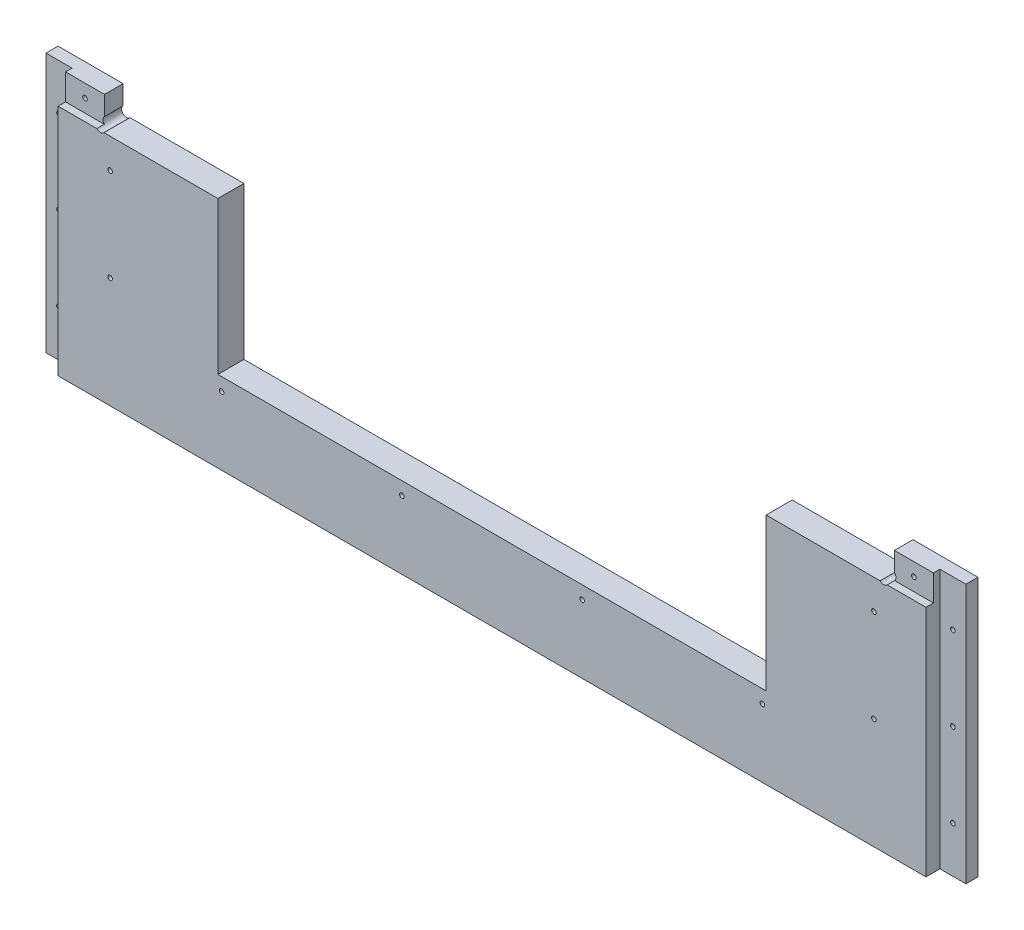
SolidWorks part; units mm, degrees
material "Pine"
ref_plane "Front Plane" through (0, 0, 0) normal (0, 0, 1) x (1, 0, 0)
ref_plane "Top Plane" through (0, 0, 0) normal (0, 1, 0) x (1, 0, 0)
ref_plane "Right Plane" through (0, 0, 0) normal (1, 0, 0) x (0, 0, -1)
sketch "Sketch1" plane through (0, 0, 0) normal (0, 0, 1) x (1, 0, 0)
  line L0 (8932.6508, -5243.5125) -> (10226.1458, -5243.5125)
  line L1 (9086.3208, -4722.0918) -> (10222.9708, -4853.7812)
  line L2 (8914.8708, -6342.0625) -> (10197.5708, -6342.0625)
  line L3 (8914.8708, -5808.6625) -> (10197.5708, -5808.6625)
  line L4 (8919.6333, -5253.0375) -> (10218.2083, -5253.0375)
  line L5 (9134.2633, -4656.1375) -> (9134.2633, -4638.3575)
  line L6 (9091.0833, -4638.3575) -> (9134.2633, -4638.3575)
  line L7 (9091.0833, -4567.2375) -> (9091.0833, -4638.3575)
  line L8 (9134.2633, -4656.1375) -> (9581.3033, -4656.1375)
  line L9 (9091.0833, -4567.2375) -> (9624.4833, -4567.2375)
  line L10 (9581.3033, -4656.1375) -> (9581.3033, -4638.3575)
  line L11 (9581.3033, -4638.3575) -> (9624.4833, -4638.3575)
  line L12 (9624.4833, -4567.2375) -> (9624.4833, -4638.3575)
  line L13 (8932.6508, -5225.7325) -> (9344.9775, -5225.7325)
  line L14 (8932.6508, -5256.2125) -> (8932.6508, -5243.5125)
  line L15 (8911.6958, -5256.2125) -> (8932.6508, -5256.2125)
  line L16 (8914.8708, -4722.0918) -> (9086.3208, -4722.0918)
  line L17 (8911.6958, -4715.5913) -> (8932.6508, -4715.5913)
  line L18 (8914.8708, -6342.0625) -> (8914.8708, -5808.6625)
  line L19 (12082.9917, -4722.0918) -> (10946.3417, -4853.7812)
  line L20 (12236.6617, -5243.5125) -> (10943.1667, -5243.5125)
  line L21 (10951.1042, -5253.0375) -> (12249.6792, -5253.0375)
  line L22 (10838.3917, -5656.2625) -> (11308.2917, -5656.2625)
  line L23 (10838.3917, -5719.7625) -> (11308.2917, -5719.7625)
  line L24 (10838.3917, -5742.5368) -> (11308.2917, -5742.5368)
  line L25 (10806.6417, -6342.0625) -> (11340.0417, -6342.0625)
  line L26 (10803.4667, -6335.7125) -> (11343.2167, -6335.7125)
  line L27 (10803.4667, -6317.9325) -> (11343.2167, -6317.9325)
  line L28 (10943.1667, -5225.7325) -> (11376.4483, -5225.7325)
  line L29 (11506.7292, -4754.5625) -> (10806.6417, -4827.5875)
  line L30 (11506.7292, -4567.2375) -> (11506.7292, -4754.5625)
  line L31 (10806.6417, -4567.2375) -> (10806.6417, -4827.5875)
  line L32 (10806.6417, -4567.2375) -> (11506.7292, -4567.2375)
  line L33 (10235.6708, -6329.3625) -> (10245.1958, -6329.3625)
  line L34 (10245.1958, -6329.3625) -> (10254.7208, -6278.5625)
  line L35 (10302.3458, -6329.3625) -> (10311.8708, -6278.5625)
  line L36 (10302.3458, -6329.3625) -> (10292.8208, -6329.3625)
  line L37 (10245.1958, -5821.3625) -> (10254.7208, -5872.1625)
  line L38 (10235.6708, -5821.3625) -> (10245.1958, -5821.3625)
  line L39 (10292.8208, -5821.3625) -> (10302.3458, -5821.3625)
  line L40 (10302.3458, -5821.3625) -> (10311.8708, -5872.1625)
  line L41 (10235.6708, -5821.3625) -> (10235.6708, -6329.3625)
  line L42 (10254.7208, -5872.1625) -> (10254.7208, -6278.5625)
  line L43 (10311.8708, -5872.1625) -> (10311.8708, -6278.5625)
  line L44 (10292.8208, -5821.3625) -> (10292.8208, -6329.3625)
  line L45 (8932.6508, -5225.7325) -> (8932.6508, -4715.5913)
  line L46 (8911.6958, -4715.5913) -> (8911.6958, -5256.2125)
  line L47 (8914.8708, -5248.275) -> (8914.8708, -4722.0918)
  line L48 (8919.6333, -5253.0375) -> (8914.8708, -5248.275)
  line L49 (8914.8708, -5145.0875) -> (8937.426, -5145.0875)
  line L50 (8914.8708, -5202.2375) -> (8937.426, -5202.2375)
  line L51 (10838.3917, -5656.2625) -> (10838.3917, -5719.7625)
  line L52 (10832.0417, -5736.1868) -> (10856.1717, -5736.1868)
  line L53 (10806.6417, -6342.0625) -> (10806.6417, -5818.7368)
  line L54 (10832.0417, -5649.9125) -> (10856.1717, -5649.9125)
  line L55 (10832.0417, -5726.1125) -> (10856.1717, -5726.1125)
  line L56 (10806.6417, -5818.7368) -> (10833.9015, -5818.7368)
  line L57 (10832.0417, -5806.0442) -> (10851.6815, -5806.0442)
  line L58 (10856.1717, -5801.5541) -> (10856.1717, -5736.1868)
  line L59 (10838.3917, -5814.2467) -> (10838.3917, -5742.5368)
  line L60 (10832.0417, -5806.0442) -> (10832.0417, -5736.1868)
  line L61 (10803.4667, -6317.9325) -> (10803.4667, -6335.7125)
  line L62 (10197.5708, -5808.6625) -> (10197.5708, -6342.0625)
  line L63 (9762.3842, -6348.4125) -> (9762.3842, -5802.3125)
  line L64 (9780.1642, -6348.4125) -> (9762.3842, -6348.4125)
  line L65 (9780.1642, -5802.3125) -> (9780.1642, -6348.4125)
  line L66 (9762.3842, -5802.3125) -> (9780.1642, -5802.3125)
  line L67 (9332.2775, -6348.4125) -> (9332.2775, -5802.3125)
  line L68 (9332.2775, -6348.4125) -> (9350.0575, -6348.4125)
  line L69 (9350.0575, -5802.3125) -> (9350.0575, -6348.4125)
  line L70 (9332.2775, -5802.3125) -> (9350.0575, -5802.3125)
  line L71 (9993.8374, -6061.075) -> (9993.8374, -6045.2418)
  line L72 (9998.5999, -6065.8375) -> (10014.4331, -6065.8375)
  line L73 (9998.5999, -6084.8875) -> (10014.4331, -6084.8875)
  line L74 (9993.8374, -6105.4832) -> (9993.8374, -6089.65)
  line L75 (9974.7874, -6105.4832) -> (9974.7874, -6089.65)
  line L76 (9954.1917, -6084.8875) -> (9970.0249, -6084.8875)
  line L77 (9974.7874, -6061.075) -> (9974.7874, -6045.2418)
  line L78 (9954.1917, -6065.8375) -> (9970.0249, -6065.8375)
  line L79 (10793.9417, -6237.2875) -> (10816.4969, -6237.2875)
  line L80 (10793.9417, -6294.4375) -> (10816.4969, -6294.4375)
  line L81 (10856.1717, -5649.9125) -> (10856.1717, -5726.1125)
  line L82 (10832.0417, -5726.1125) -> (10832.0417, -5649.9125)
  line L83 (10226.1458, -5225.7325) -> (10226.1458, -5243.5125)
  line L84 (10205.1908, -5257.8) -> (10205.1908, -4844.2499)
  line L85 (10230.9083, -4844.2499) -> (10230.9083, -5257.8)
  line L86 (10205.1908, -5257.8) -> (10230.9083, -5257.8)
  line L87 (10205.1908, -4844.2499) -> (10230.9083, -4844.2499)
  line L88 (10946.3417, -5176.8375) -> (10968.8969, -5176.8375)
  line L89 (9349.4676, -5141.9125) -> (9358.2674, -5141.9125)
  line L90 (10946.3417, -5119.6875) -> (10968.8969, -5119.6875)
  line L91 (9929.011, -4660.9635) -> (10066.0807, -4660.9635)
  line L92 (9929.011, -4678.7435) -> (10066.0807, -4678.7435)
  line L93 (10943.1667, -5225.7325) -> (10943.1667, -5243.5125)
  line L94 (10946.3417, -5248.275) -> (10951.1042, -5253.0375)
  line L95 (10946.3417, -5257.8063) -> (10946.3417, -4849.0188)
  line L96 (10964.1217, -5257.8) -> (10964.1217, -4844.2499)
  line L97 (10938.4042, -4844.2499) -> (10938.4042, -5257.8)
  line L98 (10938.4042, -5257.8) -> (10964.1217, -5257.8)
  line L99 (10964.1217, -4844.2499) -> (10938.4042, -4844.2499)
  line L100 (10344.8908, -4560.8875) -> (10369.0208, -4560.8875)
  line L101 (10344.8908, -4560.8875) -> (10369.0208, -4560.8875)
  line L102 (10800.2917, -4560.8875) -> (10824.4217, -4560.8875)
  line L103 (10200.4156, -5119.6875) -> (10222.9708, -5119.6875)
  line L104 (10200.4156, -5176.8375) -> (10222.9708, -5176.8375)
  line L105 (9344.9775, -5146.4026) -> (9344.9775, -5225.7325)
  line L106 (10344.8908, -4560.8875) -> (10344.8908, -4833.9375)
  line L107 (9792.8642, -5225.7325) -> (9792.8642, -5146.4026)
  line L108 (9362.7575, -5225.7325) -> (9775.0842, -5225.7325)
  line L109 (9680.3633, -4761.8396) -> (9680.3633, -4559.9604)
  line L110 (9656.2333, -4559.9604) -> (9680.3633, -4559.9604)
  line L111 (9656.2333, -4761.8396) -> (9680.3633, -4761.8396)
  line L112 (9656.2333, -4761.8396) -> (9656.2333, -4559.9604)
  line L113 (9779.5743, -5141.9125) -> (9788.374, -5141.9125)
  line L114 (10070.5708, -4665.4536) -> (10070.5708, -4674.2534)
  line L115 (9924.5208, -4674.2534) -> (9924.5208, -4665.4536)
  line L116 (12127.4417, -6188.3925) -> (12205.5015, -6188.3925)
  line L117 (12209.9917, -6170.6125) -> (12209.9917, -6183.9024)
  line L118 (9792.8642, -5225.7325) -> (10226.1458, -5225.7325)
  line L119 (9662.5833, -4754.5625) -> (10362.6708, -4827.5875)
  line L120 (9662.5833, -4567.2375) -> (9662.5833, -4754.5625)
  line L121 (10362.6708, -4567.2375) -> (10362.6708, -4827.5875)
  line L122 (9662.5833, -4567.2375) -> (10362.6708, -4567.2375)
  line L123 (10824.4217, -4833.9375) -> (10800.2917, -4833.9375)
  line L124 (10800.2917, -4833.9375) -> (10800.2917, -4560.8875)
  line L125 (10824.4217, -4560.8875) -> (10824.4217, -4833.9375)
  line L126 (10344.8908, -4833.9375) -> (10369.0208, -4833.9375)
  line L127 (10369.0208, -4833.9375) -> (10369.0208, -4560.8875)
  line L128 (10222.9708, -5248.275) -> (10218.2083, -5253.0375)
  line L129 (10222.9708, -5257.8063) -> (10222.9708, -4849.0188)
  line L130 (11734.6544, -5701.375) -> (11739.2301, -5701.375)
  line L131 (9362.7575, -5225.7325) -> (9362.7575, -5146.4026)
  line L132 (9775.0842, -5146.4026) -> (9775.0842, -5225.7325)
  line L133 (11761.3864, -5701.375) -> (11756.8282, -5701.375)
  line L134 (11734.6544, -5693.755) -> (11739.2301, -5693.755)
  line L135 (11761.4039, -5693.755) -> (11756.8282, -5693.755)
  line L136 (11734.6544, -5701.375) -> (11739.2301, -5701.375)
  line L137 (11744.3462, -5721.3024) -> (11744.3462, -5706.4179)
  line L138 (11751.7122, -5721.3024) -> (11751.7122, -5706.4179)
  line L139 (11740.0917, -6170.6125) -> (11740.0917, -6183.9024)
  line L140 (11689.2917, -6188.3925) -> (11822.6417, -6188.3925)
  line L141 (11689.2917, -6348.4093) -> (11689.2917, -6164.2657)
  line L142 (11689.2917, -6164.2657) -> (11746.4417, -6164.2657)
  line L143 (11746.4417, -6164.2657) -> (11746.4417, -6188.3925)
  line L144 (11689.2917, -6164.2657) -> (11746.4417, -6164.2657)
  line L145 (11340.0417, -5818.7368) -> (11340.0417, -6342.0625)
  line L146 (11290.5117, -5726.1125) -> (11314.6417, -5726.1125)
  line L147 (11290.5117, -5649.9125) -> (11290.5117, -5726.1125)
  line L148 (11340.0417, -5818.7368) -> (11312.7818, -5818.7368)
  line L149 (11314.6417, -5806.0442) -> (11295.0018, -5806.0442)
  line L150 (11290.5117, -5801.5541) -> (11290.5117, -5736.1868)
  line L151 (11308.2917, -5814.2467) -> (11308.2917, -5742.5368)
  line L152 (11314.6417, -5806.0442) -> (11314.6417, -5736.1868)
  line L153 (11290.5117, -5736.1868) -> (11314.6417, -5736.1868)
  line L154 (11848.0417, -6267.1325) -> (11962.3417, -6267.1325)
  line L155 (11962.3417, -6267.1325) -> (11962.3417, -6203.6325)
  line L156 (11343.2167, -6317.9325) -> (11343.2167, -6335.7125)
  line L157 (11365.4417, -5656.2625) -> (11365.4417, -5719.7625)
  line L158 (11365.4417, -5656.2625) -> (11479.7417, -5656.2625)
  line L159 (11778.1917, -6071.3937) -> (11802.3217, -6071.3937)
  line L160 (11314.6417, -5726.1125) -> (11314.6417, -5649.9125)
  line L161 (11314.6417, -5649.9125) -> (11290.5117, -5649.9125)
  line L162 (11308.2917, -5719.7625) -> (11308.2917, -5656.2625)
  line L163 (11689.2917, -6348.4093) -> (11713.4217, -6348.4093)
  line L164 (12203.6417, -6164.2657) -> (12260.7917, -6164.2657)
  line L165 (11713.4217, -6348.4093) -> (11713.4217, -6164.2657)
  line L166 (11695.6417, -6342.0625) -> (11695.6417, -6170.6125)
  line L167 (11695.6417, -6048.5337) -> (11699.4517, -6052.3437)
  line L168 (11822.6417, -6292.5325) -> (11822.6417, -6188.3925)
  line L169 (11695.6417, -6342.0625) -> (11695.6417, -6170.6125)
  line L170 (11848.0417, -6203.6325) -> (11962.3417, -6203.6325)
  line L171 (11848.0417, -6203.6325) -> (11848.0417, -6267.1325)
  line L172 (11987.7417, -6267.1325) -> (11987.7417, -6203.6325)
  line L173 (11784.5417, -6077.7437) -> (11784.5417, -6141.2438)
  line L174 (11517.8417, -5656.2625) -> (11632.1417, -5656.2625)
  line L175 (11632.1417, -5656.2625) -> (11632.1417, -5719.7625)
  line L176 (11632.1417, -5719.7625) -> (11517.8417, -5719.7625)
  line L177 (11517.8417, -5719.7625) -> (11517.8417, -5656.2625)
  line L178 (11692.4667, -6028.2137) -> (11692.4667, -6045.9937)
  line L179 (11695.6417, -5979.3188) -> (11718.1969, -5979.3188)
  line L180 (11695.6417, -5922.1687) -> (11718.1969, -5922.1687)
  line L181 (11821.0415, -5722.9375) -> (11821.0415, -5943.6)
  line L182 (11687.7042, -5651.5) -> (11701.9917, -5651.5)
  line L183 (11687.7042, -5651.5) -> (11687.7042, -6055.5251)
  line L184 (11687.7042, -6055.5251) -> (11701.9917, -6055.5251)
  line L185 (11701.9917, -6055.5251) -> (11701.9917, -5651.5)
  line L186 (11695.6417, -6055.2013) -> (11695.6417, -5649.595)
  line L187 (11695.6417, -5656.2625) -> (11695.6417, -6048.5337)
  line L188 (11695.6417, -6170.6125) -> (11740.0917, -6170.6125)
  line L189 (12203.6417, -6164.2657) -> (12203.6417, -6188.3925)
  line L190 (12254.4417, -6342.0625) -> (12254.4417, -6170.6125)
  line L191 (12129.0419, -5943.6) -> (12129.0419, -5722.9375)
  line L192 (12254.4417, -6048.5337) -> (12250.6317, -6052.3437)
  line L193 (12257.6167, -6045.9937) -> (12257.6167, -6028.2137)
  line L194 (12248.0917, -5651.5) -> (12262.3792, -5651.5)
  line L195 (12262.3792, -5651.5) -> (12262.3792, -6055.5251)
  line L196 (12262.3792, -6055.5251) -> (12248.0917, -6055.5251)
  line L197 (12248.0917, -6055.5251) -> (12248.0917, -5651.5)
  line L198 (12254.4417, -6141.2438) -> (12254.4417, -6077.7437)
  line L199 (12236.6617, -6164.2657) -> (12260.7917, -6164.2657)
  line L200 (12102.0417, -6267.1325) -> (11987.7417, -6267.1325)
  line L201 (11330.1865, -6237.2875) -> (11352.7417, -6237.2875)
  line L202 (11330.1865, -6294.4375) -> (11352.7417, -6294.4375)
  line L203 (11474.6617, -5851.8425) -> (11492.4417, -5851.8425)
  line L204 (11474.6617, -5808.6625) -> (11474.6617, -5851.8425)
  line L205 (11403.5417, -5808.6625) -> (11474.6617, -5808.6625)
  line L206 (11492.4417, -5851.8425) -> (11492.4417, -6298.8825)
  line L207 (11403.5417, -6342.0625) -> (11403.5417, -5808.6625)
  line L208 (11474.6617, -6298.8825) -> (11492.4417, -6298.8825)
  line L209 (11474.6617, -6342.0625) -> (11474.6617, -6298.8825)
  line L210 (11403.5417, -6342.0625) -> (11474.6617, -6342.0625)
  line L211 (11619.4417, -5851.8425) -> (11601.6617, -5851.8425)
  line L212 (11601.6617, -5808.6625) -> (11601.6617, -5851.8425)
  line L213 (11530.5417, -5808.6625) -> (11601.6617, -5808.6625)
  line L214 (11619.4417, -5851.8425) -> (11619.4417, -6298.8825)
  line L215 (11530.5417, -6342.0625) -> (11530.5417, -5808.6625)
  line L216 (11619.4417, -6298.8825) -> (11601.6617, -6298.8825)
  line L217 (11601.6617, -6342.0625) -> (11601.6617, -6298.8825)
  line L218 (11530.5417, -6342.0625) -> (11601.6617, -6342.0625)
  line L219 (11479.7417, -5719.7625) -> (11479.7417, -5656.2625)
  line L220 (11365.4417, -5719.7625) -> (11479.7417, -5719.7625)
  line L221 (11778.1917, -6147.5937) -> (11802.3217, -6147.5937)
  line L222 (11802.3217, -6071.3937) -> (11802.3217, -6147.5937)
  line L223 (11778.1917, -6147.5937) -> (11778.1917, -6071.3937)
  line L224 (12254.4417, -5922.1687) -> (12231.8865, -5922.1687)
  line L225 (12254.4417, -5979.3188) -> (12231.8865, -5979.3188)
  line L226 (12254.4417, -6055.2013) -> (12254.4417, -5649.595)
  line L227 (12254.4417, -6048.5337) -> (12254.4417, -5656.2625)
  line L228 (11841.6917, -5702.2873) -> (12108.3917, -5702.2873)
  line L229 (11822.6417, -6292.5325) -> (12127.4417, -6292.5325)
  line L230 (12127.4417, -6292.5325) -> (12127.4417, -6188.3925)
  line L231 (12254.4417, -6170.6125) -> (12209.9917, -6170.6125)
  line L232 (11695.6417, -6342.0625) -> (12254.4417, -6342.0625)
  line L233 (12236.6617, -6348.4093) -> (12260.7917, -6348.4093)
  line L234 (12260.7917, -6348.4093) -> (12260.7917, -6164.2657)
  line L235 (12236.6617, -6348.4093) -> (12236.6617, -6164.2657)
  line L236 (12102.0417, -6203.6325) -> (12102.0417, -6267.1325)
  line L237 (11987.7417, -6203.6325) -> (12102.0417, -6203.6325)
  line L238 (12236.6617, -6147.5937) -> (12236.6617, -6071.3937)
  line L239 (12203.6417, -6188.3925) -> (12260.7917, -6188.3925)
  line L240 (11098.7417, -4665.4536) -> (11098.7417, -4674.2534)
  line L241 (11394.2283, -5146.4026) -> (11394.2283, -5225.7325)
  line L242 (11376.4483, -5225.7325) -> (11376.4483, -5146.4026)
  line L243 (11394.2283, -5225.7325) -> (11806.555, -5225.7325)
  line L244 (11841.6917, -5964.2502) -> (12108.3917, -5964.2502)
  line L245 (12236.6617, -6147.5937) -> (12260.7917, -6147.5937)
  line L246 (12236.6617, -5256.2125) -> (12236.6617, -5243.5125)
  line L247 (12260.7917, -6147.5937) -> (12260.7917, -6071.3937)
  line L248 (12260.7917, -6071.3937) -> (12236.6617, -6071.3937)
  line L249 (12254.4417, -6077.7437) -> (11784.5417, -6077.7437)
  line L250 (11784.5417, -6141.2438) -> (12254.4417, -6141.2438)
  line L252 (12254.4417, -5656.2625) -> (11695.6417, -5656.2625)
  line L253 (11699.4517, -6052.3437) -> (12250.6317, -6052.3437)
  line L254 (11692.4667, -6045.9937) -> (12257.6167, -6045.9937)
  line L255 (11692.4667, -6028.2137) -> (12257.6167, -6028.2137)
  line L256 (11824.335, -5146.4026) -> (11824.335, -5225.7325)
  line L257 (11811.0451, -5141.9125) -> (11819.8449, -5141.9125)
  line L258 (11244.7917, -4674.2534) -> (11244.7917, -4665.4536)
  line L259 (11806.555, -5225.7325) -> (11806.555, -5146.4026)
  line L260 (11488.9492, -4761.8396) -> (11488.9492, -4559.9604)
  line L261 (11488.9492, -4559.9604) -> (11513.0792, -4559.9604)
  line L262 (11488.9492, -4761.8396) -> (11513.0792, -4761.8396)
  line L263 (11513.0792, -4761.8396) -> (11513.0792, -4559.9604)
  line L264 (11240.3015, -4660.9635) -> (11103.2318, -4660.9635)
  line L265 (11103.2318, -4678.7435) -> (11240.3015, -4678.7435)
  line L266 (12236.6617, -5225.7325) -> (12236.6617, -4715.5913)
  line L267 (12257.6167, -4715.5913) -> (12257.6167, -5256.2125)
  line L268 (12254.4417, -5248.275) -> (12254.4417, -4722.0918)
  line L269 (12236.6617, -5225.7325) -> (11824.335, -5225.7325)
  line L270 (12035.0492, -4656.1375) -> (12035.0492, -4638.3575)
  line L271 (12078.2292, -4638.3575) -> (12035.0492, -4638.3575)
  line L272 (12078.2292, -4567.2375) -> (12078.2292, -4638.3575)
  line L273 (12035.0492, -4656.1375) -> (11588.0092, -4656.1375)
  line L274 (11544.8292, -4567.2375) -> (12078.2292, -4567.2375)
  line L275 (11588.0092, -4656.1375) -> (11588.0092, -4638.3575)
  line L276 (11544.8292, -4638.3575) -> (11588.0092, -4638.3575)
  line L277 (11544.8292, -4567.2375) -> (11544.8292, -4638.3575)
  line L278 (12249.6792, -5253.0375) -> (12254.4417, -5248.275)
  line L280 (12257.6167, -5256.2125) -> (12236.6617, -5256.2125)
  line L281 (12231.8865, -5145.0875) -> (12254.4417, -5145.0875)
  line L282 (12231.8865, -5202.2375) -> (12254.4417, -5202.2375)
  line L283 (12236.6617, -4715.5913) -> (12257.6167, -4715.5913)
  line L284 (12082.9917, -4722.0918) -> (12254.4417, -4722.0918)
  line L285 (11380.9385, -5141.9125) -> (11389.7382, -5141.9125)
  circle A0 centre (8923.7608, -4778.9042) radius 1.5875
  circle A1 centre (9062.6598, -4736.3765) radius 2.3685
  circle A2 centre (9051.3958, -6281.7375) radius 22.225
  circle A3 centre (9083.1458, -6249.9875) radius 1.5875
  circle A4 centre (9083.1458, -6313.4875) radius 1.5875
  circle A5 centre (9019.6458, -6249.9875) radius 1.5875
  circle A6 centre (9019.6458, -6313.4875) radius 1.5875
  circle A7 centre (8972.3383, -5202.2375) radius 1.5875
  circle A8 centre (8923.7608, -5015.9708) radius 1.5875
  circle A9 centre (8923.7608, -5134.5042) radius 1.5875
  circle A10 centre (9054.5708, -5234.6225) radius 1.5875
  circle A11 centre (8923.7608, -4897.4375) radius 1.5875
  circle A12 centre (8972.3383, -5087.9375) radius 1.5875
  circle A13 centre (8972.3383, -5145.0875) radius 1.5875
  circle A14 centre (10847.2817, -5668.9625) radius 1.5875
  circle A15 centre (10847.2817, -5707.0625) radius 1.5875
  circle A16 centre (10847.2817, -5755.2368) radius 1.5875
  circle A17 centre (10851.4092, -6237.2875) radius 1.5875
  circle A18 centre (10851.4092, -6294.4375) radius 1.5875
  circle A19 centre (10847.2817, -5793.3442) radius 1.5875
  arc A20 (10833.9015, -5818.7368) -> (10838.3917, -5814.2467) centre (10836.1466, -5816.4918) ccw
  arc A21 (10851.6815, -5806.0442) -> (10856.1717, -5801.5541) centre (10853.9266, -5803.7992) ccw
  circle A22 centre (10882.8417, -6040.4375) radius 1.5875
  circle A23 centre (10882.8417, -6218.2375) radius 1.5875
  circle A24 centre (10882.8417, -5862.6375) radius 1.5875
  circle A25 centre (10908.2417, -6326.8225) radius 1.5875
  circle A26 centre (10908.2417, -6326.8225) radius 1.5875
  circle A27 centre (10851.4092, -6180.1375) radius 1.5875
  circle A28 centre (10815.5317, -4783.4231) radius 1.5875
  circle A29 centre (10815.5317, -4696.9488) radius 1.5875
  circle A30 centre (10815.5317, -4610.4746) radius 1.5875
  circle A31 centre (10979.1323, -4867.0082) radius 2.3685
  circle A32 centre (10190.1802, -4867.0082) radius 2.3685
  circle A33 centre (10955.2317, -4929.9812) radius 1.5875
  circle A34 centre (10955.2317, -5031.5812) radius 1.5875
  circle A35 centre (10214.0808, -4929.9812) radius 1.5875
  circle A36 centre (10214.0808, -5031.5812) radius 1.5875
  circle A37 centre (9341.1675, -6265.8625) radius 1.5875
  circle A38 centre (9771.2742, -5884.8625) radius 1.5875
  circle A39 centre (9771.2742, -6138.8625) radius 1.5875
  circle A40 centre (9771.2742, -6011.8625) radius 1.5875
  arc A41 (10036.2287, -6113.8083) -> (10051.3426, -6111.6033) centre (10042.9639, -6107.0732) ccw
  arc A42 (10051.3426, -6111.6033) -> (10051.3426, -6039.1217) centre (9984.3124, -6075.3625) ccw
  arc A43 (10051.3426, -6039.1217) -> (10036.2287, -6036.9167) centre (10042.9639, -6043.6518) ccw
  arc A44 (10034.5851, -6102.5431) -> (10034.5851, -6048.1819) centre (9984.3124, -6075.3625) ccw
  arc A45 (10034.5851, -6102.5431) -> (10036.2287, -6113.8083) centre (10042.9639, -6107.0732) ccw
  arc A46 (10036.2287, -6036.9167) -> (10034.5851, -6048.1819) centre (10042.9639, -6043.6518) ccw
  arc A47 (9945.8666, -6127.2787) -> (9948.0717, -6142.3927) centre (9952.6018, -6134.0139) ccw
  arc A48 (9948.0717, -6142.3927) -> (10020.5532, -6142.3927) centre (9984.3124, -6075.3625) ccw
  arc A49 (10020.5532, -6142.3927) -> (10022.7583, -6127.2787) centre (10016.0231, -6134.0139) ccw
  arc A50 (9957.1319, -6125.6352) -> (10011.493, -6125.6352) centre (9984.3124, -6075.3625) ccw
  arc A51 (9957.1319, -6125.6352) -> (9945.8666, -6127.2787) centre (9952.6018, -6134.0139) ccw
  arc A52 (10022.7583, -6127.2787) -> (10011.493, -6125.6352) centre (10016.0231, -6134.0139) ccw
  arc A53 (9932.3962, -6036.9167) -> (9917.2822, -6039.1217) centre (9925.661, -6043.6518) ccw
  arc A54 (9917.2822, -6039.1217) -> (9917.2822, -6111.6033) centre (9984.3124, -6075.3625) ccw
  arc A55 (9917.2822, -6111.6033) -> (9932.3962, -6113.8083) centre (9925.661, -6107.0732) ccw
  arc A56 (9934.0398, -6048.1819) -> (9934.0398, -6102.5431) centre (9984.3124, -6075.3625) ccw
  arc A57 (9934.0398, -6048.1819) -> (9932.3962, -6036.9167) centre (9925.661, -6043.6518) ccw
  arc A58 (9932.3962, -6113.8083) -> (9934.0398, -6102.5431) centre (9925.661, -6107.0732) ccw
  arc A59 (9945.8666, -6023.4463) -> (9957.1319, -6025.0898) centre (9952.6018, -6016.7111) ccw
  arc A60 (10011.493, -6025.0898) -> (10022.7583, -6023.4463) centre (10016.0231, -6016.7111) ccw
  arc A61 (10011.493, -6025.0898) -> (9957.1319, -6025.0898) centre (9984.3124, -6075.3625) ccw
  arc A62 (9948.0717, -6008.3323) -> (9945.8666, -6023.4463) centre (9952.6018, -6016.7111) ccw
  arc A63 (10020.5532, -6008.3323) -> (9948.0717, -6008.3323) centre (9984.3124, -6075.3625) ccw
  arc A64 (10022.7583, -6023.4463) -> (10020.5532, -6008.3323) centre (10016.0231, -6016.7111) ccw
  arc A65 (10005.0943, -6187.7574) -> (10096.7073, -6096.1443) centre (9984.3124, -6075.3625) ccw
  arc A66 (9993.8374, -6178.3911) -> (10005.0943, -6187.7574) centre (10003.3624, -6178.3911) ccw
  arc A67 (10001.6306, -6169.0249) -> (10077.9748, -6092.6807) centre (9984.3124, -6075.3625) ccw
  arc A68 (10087.3411, -6084.8875) -> (10077.9748, -6092.6807) centre (10087.3411, -6094.4125) ccw
  arc A69 (10001.6306, -6169.0249) -> (9993.8374, -6178.3911) centre (10003.3624, -6178.3911) ccw
  arc A70 (9963.5306, -6187.7574) -> (9974.7874, -6178.3911) centre (9965.2624, -6178.3911) ccw
  arc A71 (9871.9176, -6096.1443) -> (9963.5306, -6187.7574) centre (9984.3124, -6075.3625) ccw
  arc A72 (9881.2838, -6084.8875) -> (9871.9176, -6096.1443) centre (9881.2838, -6094.4125) ccw
  arc A73 (9890.65, -6092.6807) -> (9966.9943, -6169.0249) centre (9984.3124, -6075.3625) ccw
  arc A74 (9974.7874, -6178.3911) -> (9966.9943, -6169.0249) centre (9965.2624, -6178.3911) ccw
  arc A75 (9890.65, -6092.6807) -> (9881.2838, -6084.8875) centre (9881.2838, -6094.4125) ccw
  arc A76 (9871.9176, -6054.5807) -> (9881.2838, -6065.8375) centre (9881.2838, -6056.3125) ccw
  arc A77 (9963.5306, -5962.9676) -> (9871.9176, -6054.5807) centre (9984.3124, -6075.3625) ccw
  arc A78 (9974.7874, -5972.3339) -> (9963.5306, -5962.9676) centre (9965.2624, -5972.3339) ccw
  arc A79 (9966.9943, -5981.7001) -> (9890.65, -6058.0443) centre (9984.3124, -6075.3625) ccw
  arc A80 (9881.2838, -6065.8375) -> (9890.65, -6058.0443) centre (9881.2838, -6056.3125) ccw
  arc A81 (9966.9943, -5981.7001) -> (9974.7874, -5972.3339) centre (9965.2624, -5972.3339) ccw
  arc A82 (10077.9748, -6058.0443) -> (10087.3411, -6065.8375) centre (10087.3411, -6056.3125) ccw
  arc A83 (9993.8374, -5972.3339) -> (10001.6306, -5981.7001) centre (10003.3624, -5972.3339) ccw
  arc A84 (10077.9748, -6058.0443) -> (10001.6306, -5981.7001) centre (9984.3124, -6075.3625) ccw
  arc A85 (10087.3411, -6065.8375) -> (10096.7073, -6054.5807) centre (10087.3411, -6056.3125) ccw
  arc A86 (10096.7073, -6054.5807) -> (10005.0943, -5962.9676) centre (9984.3124, -6075.3625) ccw
  arc A87 (10005.0943, -5962.9676) -> (9993.8374, -5972.3339) centre (10003.3624, -5972.3339) ccw
  arc A88 (10014.4331, -6065.8375) -> (10018.7361, -6059.0339) centre (10014.4331, -6061.075) ccw
  arc A89 (10018.7361, -6059.0339) -> (10000.641, -6040.9388) centre (9984.3124, -6075.3625) ccw
  arc A90 (10000.641, -6040.9388) -> (9993.8374, -6045.2418) centre (9998.5999, -6045.2418) ccw
  arc A91 (9993.8374, -6061.075) -> (9998.5999, -6065.8375) centre (9998.5999, -6061.075) ccw
  arc A92 (9993.8374, -6105.4832) -> (10000.641, -6109.7862) centre (9998.5999, -6105.4832) ccw
  arc A93 (10000.641, -6109.7862) -> (10018.7361, -6091.6911) centre (9984.3124, -6075.3625) ccw
  arc A94 (10018.7361, -6091.6911) -> (10014.4331, -6084.8875) centre (10014.4331, -6089.65) ccw
  arc A95 (9998.5999, -6084.8875) -> (9993.8374, -6089.65) centre (9998.5999, -6089.65) ccw
  arc A96 (9954.1917, -6084.8875) -> (9949.8888, -6091.6911) centre (9954.1917, -6089.65) ccw
  arc A97 (9949.8888, -6091.6911) -> (9967.9839, -6109.7862) centre (9984.3124, -6075.3625) ccw
  arc A98 (9967.9839, -6109.7862) -> (9974.7874, -6105.4832) centre (9970.0249, -6105.4832) ccw
  arc A99 (9974.7874, -6089.65) -> (9970.0249, -6084.8875) centre (9970.0249, -6089.65) ccw
  arc A100 (9970.0249, -6065.8375) -> (9974.7874, -6061.075) centre (9970.0249, -6061.075) ccw
  arc A101 (9949.8888, -6059.0339) -> (9954.1917, -6065.8375) centre (9954.1917, -6061.075) ccw
  arc A102 (9967.9839, -6040.9388) -> (9949.8888, -6059.0339) centre (9984.3124, -6075.3625) ccw
  arc A103 (9974.7874, -6045.2418) -> (9967.9839, -6040.9388) centre (9970.0249, -6045.2418) ccw
  arc A104 (10096.7073, -6096.1443) -> (10087.3411, -6084.8875) centre (10087.3411, -6094.4125) ccw
  circle A105 centre (9771.2742, -6265.8625) radius 1.5875
  circle A106 centre (9341.1675, -5884.8625) radius 1.5875
  circle A107 centre (9341.1675, -6138.8625) radius 1.5875
  circle A108 centre (9341.1675, -6011.8625) radius 1.5875
  circle A109 centre (11037.2315, -4887.5494) radius 15.0812
  arc A110 (9349.4676, -5141.9125) -> (9344.9775, -5146.4026) centre (9347.2226, -5144.1576) ccw
  arc A111 (9362.7575, -5146.4026) -> (9358.2674, -5141.9125) centre (9360.5124, -5144.1576) ccw
  circle A112 centre (9946.7458, -4669.8535) radius 1.5875
  arc A113 (9924.5208, -4674.2534) -> (9929.011, -4678.7435) centre (9926.7659, -4676.4984) ccw
  circle A114 centre (11003.8092, -5176.8375) radius 1.5875
  circle A115 centre (11003.8092, -5119.6875) radius 1.5875
  circle A116 centre (10353.7808, -4696.9488) radius 1.5875
  circle A117 centre (10353.7808, -4610.4746) radius 1.5875
  circle A118 centre (10353.7808, -4783.4231) radius 1.5875
  circle A119 centre (11003.8092, -5062.5375) radius 1.5875
  circle A120 centre (9353.8675, -5160.9625) radius 1.5875
  circle A121 centre (9638.7708, -5234.6225) radius 1.5875
  circle A122 centre (9671.4733, -4724.1144) radius 1.5875
  circle A123 centre (9671.4733, -4661.3637) radius 1.5875
  circle A124 centre (9671.4733, -4598.6129) radius 1.5875
  arc A125 (9792.8642, -5146.4026) -> (9788.374, -5141.9125) centre (9790.6191, -5144.1576) ccw
  arc A126 (9779.5743, -5141.9125) -> (9775.0842, -5146.4026) centre (9777.3292, -5144.1576) ccw
  circle A127 centre (10048.3458, -4669.8535) radius 1.5875
  arc A128 (10070.5708, -4665.4536) -> (10066.0807, -4660.9635) centre (10068.3258, -4663.2086) ccw
  arc A129 (10066.0807, -4678.7435) -> (10070.5708, -4674.2534) centre (10068.3258, -4676.4984) ccw
  circle A130 centre (9997.5458, -4669.8535) radius 1.5875
  arc A131 (9929.011, -4660.9635) -> (9924.5208, -4665.4536) centre (9926.7659, -4663.2086) ccw
  circle A132 centre (10132.081, -4887.5494) radius 15.0812
  circle A133 centre (10165.5033, -5176.8375) radius 1.5875
  circle A134 centre (10165.5033, -5119.6875) radius 1.5875
  circle A135 centre (9486.3708, -5234.6225) radius 1.5875
  circle A136 centre (10165.5033, -5062.5375) radius 1.5875
  circle A137 centre (9206.9708, -5234.6225) radius 1.5875
  circle A138 centre (10070.5708, -5234.6225) radius 1.5875
  circle A139 centre (9918.1708, -5234.6225) radius 1.5875
  circle A140 centre (9783.9742, -5160.9625) radius 1.5875
  circle A141 centre (9783.9742, -5193.9825) radius 1.5875
  circle A142 centre (9353.8675, -5193.9825) radius 1.5875
  circle A143 centre (11073.3417, -6326.8225) radius 1.5875
  circle A144 centre (11073.3417, -6326.8225) radius 1.5875
  circle A145 centre (11295.2742, -6180.1375) radius 1.5875
  circle A146 centre (11295.2742, -6294.4375) radius 1.5875
  circle A147 centre (11295.2742, -6237.2875) radius 1.5875
  circle A148 centre (11975.0417, -5692.775) radius 3.4925
  circle A149 centre (11263.8417, -5862.6375) radius 1.5875
  arc A150 (11739.2301, -5701.375) -> (11744.3462, -5706.4179) centre (11748.0292, -5697.565) ccw
  arc A151 (11751.7122, -5706.4179) -> (11756.8282, -5701.375) centre (11748.0292, -5697.565) ccw
  arc A152 (11744.3462, -5721.3024) -> (11751.7122, -5721.3024) centre (11748.0292, -5725.505) ccw
  arc A153 (11734.6544, -5693.755) -> (11724.9787, -5697.565) centre (11730.5667, -5697.565) ccw
  arc A154 (11756.8282, -5693.755) -> (11739.2301, -5693.755) centre (11748.0292, -5697.565) ccw
  arc A155 (11724.9787, -5697.565) -> (11734.6544, -5701.375) centre (11730.5667, -5697.565) ccw
  arc A156 (11761.3864, -5701.375) -> (11771.0797, -5697.565) centre (11765.4842, -5697.565) ccw
  arc A157 (11771.0797, -5697.565) -> (11761.4039, -5693.755) centre (11765.4917, -5697.565) ccw
  arc A158 (11740.0917, -6183.9024) -> (11744.5818, -6188.3925) centre (11742.3367, -6186.1474) ccw
  arc A159 (12205.5015, -6188.3925) -> (12209.9917, -6183.9024) centre (12207.7466, -6186.1474) ccw
  circle A160 centre (11299.4017, -5793.3442) radius 1.5875
  arc A161 (11308.2917, -5814.2467) -> (11312.7818, -5818.7368) centre (11310.5367, -5816.4918) ccw
  arc A162 (11290.5117, -5801.5541) -> (11295.0018, -5806.0442) centre (11292.7567, -5803.7992) ccw
  circle A163 centre (11704.5317, -6314.149) radius 1.5875
  circle A164 centre (11748.9817, -6208.7125) radius 1.5875
  circle A165 centre (11263.8417, -6218.2375) radius 1.5875
  circle A166 centre (11263.8417, -6040.4375) radius 1.5875
  circle A167 centre (11238.4417, -6326.8225) radius 1.5875
  circle A168 centre (11238.4417, -6326.8225) radius 1.5875
  circle A169 centre (11299.4017, -5668.9625) radius 1.5875
  circle A170 centre (11299.4017, -5707.0625) radius 1.5875
  circle A171 centre (11726.7567, -6179.5025) radius 1.5875
  circle A172 centre (11704.5317, -6199.3198) radius 1.5875
  circle A173 centre (11748.9817, -6272.2125) radius 1.5875
  circle A174 centre (11704.5317, -6256.7344) radius 1.5875
  circle A175 centre (11299.4017, -5755.2368) radius 1.5875
  circle A176 centre (11913.4467, -6301.4225) radius 1.5875
  circle A177 centre (11790.2567, -6301.4225) radius 1.5875
  circle A178 centre (11793.4317, -6128.5437) radius 1.5875
  circle A179 centre (11753.1092, -5865.0188) radius 1.5875
  circle A180 centre (11809.9417, -6037.1038) radius 1.5875
  circle A181 centre (11809.9417, -6037.1038) radius 1.5875
  circle A182 centre (11753.1092, -5922.1687) radius 1.5875
  circle A183 centre (11975.0417, -5973.7625) radius 3.4925
  circle A184 centre (11975.0417, -6037.1038) radius 1.5875
  circle A185 centre (11753.1092, -5979.3188) radius 1.5875
  circle A186 centre (11975.0417, -6037.1038) radius 1.5875
  arc A187 (11841.6917, -5702.2873) -> (11821.0415, -5722.9375) centre (11841.6917, -5722.9375) ccw
  circle A188 centre (11811.5292, -5833.2687) radius 3.4925
  arc A189 (11821.0415, -5943.6) -> (11841.6917, -5964.2502) centre (11841.6917, -5943.6) ccw
  circle A190 centre (12196.9742, -5865.0188) radius 1.5875
  arc A191 (12129.0419, -5722.9375) -> (12108.3917, -5702.2873) centre (12108.3917, -5722.9375) ccw
  circle A192 centre (12036.6367, -6301.4225) radius 1.5875
  circle A193 centre (12159.8267, -6301.4225) radius 1.5875
  circle A194 centre (12138.5542, -5833.2687) radius 3.4925
  circle A195 centre (12197.2917, -5761.0375) radius 15.0812
  circle A196 centre (11793.4317, -6090.4437) radius 1.5875
  circle A197 centre (12196.9742, -5922.1687) radius 1.5875
  arc A198 (12108.3917, -5964.2502) -> (12129.0419, -5943.6) centre (12108.3917, -5943.6) ccw
  circle A199 centre (12196.9742, -5979.3188) radius 1.5875
  circle A200 centre (12201.1017, -6272.2125) radius 1.5875
  circle A201 centre (12245.5517, -6314.149) radius 1.5875
  circle A202 centre (12245.5517, -6256.7344) radius 1.5875
  circle A203 centre (12201.1017, -6208.7125) radius 1.5875
  circle A204 centre (12223.3267, -6179.5025) radius 1.5875
  circle A205 centre (12245.5517, -6199.3198) radius 1.5875
  circle A206 centre (11171.7667, -4669.8535) radius 1.5875
  circle A207 centre (11222.5667, -4669.8535) radius 1.5875
  arc A208 (11240.3015, -4678.7435) -> (11244.7917, -4674.2534) centre (11242.5466, -4676.4984) ccw
  circle A209 centre (11385.3383, -5193.9825) radius 1.5875
  circle A210 centre (12106.6527, -4736.3765) radius 2.3685
  circle A211 centre (12140.1417, -6037.1038) radius 1.5875
  circle A212 centre (12140.1417, -6037.1038) radius 1.5875
  circle A213 centre (12245.5517, -6090.4437) radius 1.5875
  circle A214 centre (12245.5517, -6128.5437) radius 1.5875
  circle A215 centre (11385.3383, -5160.9625) radius 1.5875
  arc A216 (11824.335, -5146.4026) -> (11819.8449, -5141.9125) centre (11822.0899, -5144.1576) ccw
  arc A217 (11811.0451, -5141.9125) -> (11806.555, -5146.4026) centre (11808.8001, -5144.1576) ccw
  circle A218 centre (11815.445, -5193.9825) radius 1.5875
  circle A219 centre (11815.445, -5160.9625) radius 1.5875
  circle A220 centre (11530.5417, -5234.6225) radius 1.5875
  circle A221 centre (11962.3417, -5234.6225) radius 1.5875
  arc A222 (11244.7917, -4665.4536) -> (11240.3015, -4660.9635) centre (11242.5466, -4663.2086) ccw
  circle A223 centre (11682.9417, -5234.6225) radius 1.5875
  circle A224 centre (11497.8392, -4724.1144) radius 1.5875
  circle A225 centre (11497.8392, -4661.3637) radius 1.5875
  circle A226 centre (11497.8392, -4598.6129) radius 1.5875
  circle A227 centre (11120.9667, -4669.8535) radius 1.5875
  arc A228 (11103.2318, -4660.9635) -> (11098.7417, -4665.4536) centre (11100.9867, -4663.2086) ccw
  arc A229 (11098.7417, -4674.2534) -> (11103.2318, -4678.7435) centre (11100.9867, -4676.4984) ccw
  circle A230 centre (12196.9742, -5202.2375) radius 1.5875
  circle A231 centre (12245.5517, -5015.9708) radius 1.5875
  circle A232 centre (12245.5517, -5134.5042) radius 1.5875
  circle A233 centre (12114.7417, -5234.6225) radius 1.5875
  circle A234 centre (12245.5517, -4897.4375) radius 1.5875
  circle A235 centre (12245.5517, -4778.9042) radius 1.5875
  circle A236 centre (12196.9742, -5087.9375) radius 1.5875
  circle A237 centre (12196.9742, -5145.0875) radius 1.5875
  circle A238 centre (11098.7417, -5234.6225) radius 1.5875
  circle A239 centre (11251.1417, -5234.6225) radius 1.5875
  arc A240 (11380.9385, -5141.9125) -> (11376.4483, -5146.4026) centre (11378.6934, -5144.1576) ccw
  arc A241 (11394.2283, -5146.4026) -> (11389.7382, -5141.9125) centre (11391.9833, -5144.1576) ccw
sketch "CabCapOutline" plane through (0, 0, 0) normal (0, 0, 1) x (1, 0, 0)
  line L0 (12324.2917, -6347.9762) -> (12324.2917, -6170.6125)
  line L1 (12324.2917, -6170.6125) -> (12279.8417, -6170.6125)
  line L2 (12279.8417, -6170.6125) -> (12279.8417, -6188.3925)
  line L3 (12279.8417, -6188.3925) -> (12197.2917, -6188.3925)
  line L4 (12197.2917, -6188.3925) -> (12197.2917, -6292.5325)
  line L5 (12197.2917, -6292.5325) -> (11822.6417, -6292.5325)
  line L6 (11822.6417, -6292.5325) -> (11822.6417, -6188.3925)
  line L7 (11822.6417, -6188.3925) -> (11740.0917, -6188.3925)
  line L8 (11740.0917, -6188.3925) -> (11740.0917, -6170.6125)
  line L9 (11740.0917, -6170.6125) -> (11695.6417, -6170.6125)
  line L10 (11695.6417, -6170.6125) -> (11695.6417, -6347.9762)
  line L11 (11695.6417, -6347.9762) -> (12324.2917, -6347.9762)
  dimension "D2" = 104.14
  dimension "CabBack_Thickness" = 17.78
  dimension "CabCap_Width" = 628.65
  dimension "D5" = 44.45
  dimension "D6" = 82.55
extrude "CabCapOutline_Thickness" add sketch "CabCapOutline" against normal blind 17.78
sketch "Sketch3" plane through (0, 0, 0) normal (0, 0, 1) x (1, 0, 0)
  line L0 (11740.0917, -6188.3925) -> (11740.0917, -6170.6125)
  line L1 (11740.0917, -6170.6125) -> (11695.6417, -6170.6125)
  line L2 (11695.6417, -6170.6125) -> (11695.6417, -6188.3925)
  line L3 (11695.6417, -6188.3925) -> (11740.0917, -6188.3925)
  line L4 (12279.8417, -6170.6125) -> (12324.2917, -6170.6125)
  line L5 (12324.2917, -6170.6125) -> (12324.2917, -6188.3925)
  line L6 (12324.2917, -6188.3925) -> (12279.8417, -6188.3925)
  line L7 (12279.8417, -6188.3925) -> (12279.8417, -6170.6125)
  line L8 (11695.6417, -6170.6125) -> (11695.6417, -6347.9762) construction
  line L9 (12324.2917, -6347.9762) -> (12324.2917, -6170.6125) construction
  line L10 (12279.8417, -6170.6125) -> (12279.8417, -6188.3925) construction
  line L11 (12279.8417, -6188.3925) -> (12197.2917, -6188.3925) construction
extrude "CapBackLedge_Depth" cut sketch "Sketch3" against normal blind 5.08
sketch "CabSideLedgeCuts" plane through (0, 0, 0) normal (0, 0, 1) x (1, 0, 0)
  line L0 (11695.6417, -6347.9762) -> (11713.4217, -6347.9762)
  line L1 (11713.4217, -6347.9762) -> (11713.4217, -6170.6125)
  line L2 (11713.4217, -6170.6125) -> (11695.6417, -6170.6125)
  line L3 (11695.6417, -6170.6125) -> (11695.6417, -6347.9762)
  line L4 (12306.5117, -6347.9762) -> (12324.2917, -6347.9762)
  line L5 (12324.2917, -6347.9762) -> (12324.2917, -6170.6125)
  line L6 (12324.2917, -6170.6125) -> (12306.5117, -6170.6125)
  line L7 (12306.5117, -6170.6125) -> (12306.5117, -6347.9762)
  line L8 (11695.6417, -6347.9762) -> (12324.2917, -6347.9762) construction
  line L9 (11695.6417, -6170.6125) -> (11740.0917, -6170.6125) construction
  line L10 (12324.2917, -6170.6125) -> (12279.8417, -6170.6125) construction
  dimension "CabSideRight_Thickness" = 17.78
  dimension "CabSideLeft_Thickness" = 17.78
extrude "CabSideLedge_Depth" cut sketch "CabSideLedgeCuts" against normal blind 9.525
sketch "Sketch5" plane through (0, 0, 0) normal (0, 0, 1) x (1, 0, 0)
  line L0 (11740.0917, -6188.3925) -> (11742.3367, -6186.1474) construction
  line L1 (11822.6417, -6188.3925) -> (11713.4217, -6188.3925) construction
  line L2 (12279.8417, -6188.3925) -> (12277.5966, -6186.1474) construction
  line L3 (12306.5117, -6188.3925) -> (12197.2917, -6188.3925) construction
  line L4 (11948.3717, -6301.4225) -> (12071.5617, -6301.4225) construction
  line L5 (11825.1817, -6301.4225) -> (11948.3717, -6301.4225) construction
  line L6 (12071.5617, -6301.4225) -> (12194.7517, -6301.4225) construction
  line L7 (12009.9667, -6292.5325) -> (12009.9667, -6301.4225) construction
  line L8 (11695.6417, -6259.2944) -> (11713.4217, -6259.2944) construction
  line L9 (12197.2917, -6292.5325) -> (11822.6417, -6292.5325) construction
  line L10 (11748.9817, -6208.7125) -> (11748.9817, -6272.2125) construction
  line L11 (11748.9817, -6240.4625) -> (11822.6417, -6240.4625) construction
  line L12 (11822.6417, -6292.5325) -> (11822.6417, -6188.3925) construction
  line L13 (12270.9517, -6208.7125) -> (12270.9517, -6272.2125) construction
  line L14 (12293.1767, -6188.3925) -> (12293.1767, -6170.6125) construction
  line L15 (12270.9517, -6240.4625) -> (12197.2917, -6240.4625) construction
  line L16 (12197.2917, -6188.3925) -> (12197.2917, -6292.5325) construction
  line L17 (12279.8417, -6188.3925) -> (12306.5117, -6188.3925) construction
  line L18 (12306.5117, -6170.6125) -> (12279.8417, -6170.6125) construction
  line L19 (11726.7567, -6188.3925) -> (11726.7567, -6170.6125) construction
  line L20 (11695.6417, -6170.6125) -> (11695.6417, -6347.9762) construction
  line L21 (11713.4217, -6188.3925) -> (11740.0917, -6188.3925) construction
  line L22 (11740.0917, -6170.6125) -> (11713.4217, -6170.6125) construction
  line L23 (12324.2917, -6259.2944) -> (12306.5117, -6259.2944) construction
  line L24 (12324.2917, -6347.9762) -> (12324.2917, -6170.6125) construction
  line L25 (12306.5117, -6170.6125) -> (12306.5117, -6347.9762) construction
  line L26 (12315.4017, -6316.4444) -> (12315.4017, -6259.2944) construction
  line L27 (12315.4017, -6259.2944) -> (12315.4017, -6202.1444) construction
  line L28 (11713.4217, -6347.9762) -> (11713.4217, -6170.6125) construction
  line L29 (11704.5317, -6316.4444) -> (11704.5317, -6259.2944) construction
  line L30 (11704.5317, -6259.2944) -> (11704.5317, -6202.1444) construction
  circle A0 centre (11704.5317, -6316.4444) radius 1.5875
  circle A1 centre (11704.5317, -6259.2944) radius 1.5875
  circle A2 centre (11704.5317, -6202.1444) radius 1.5875
  circle A3 centre (11726.7567, -6179.5025) radius 1.5875
  circle A4 centre (11748.9817, -6208.7125) radius 1.5875
  circle A5 centre (11748.9817, -6272.2125) radius 1.5875
  circle A6 centre (11825.1817, -6301.4225) radius 1.5875
  circle A7 centre (11948.3717, -6301.4225) radius 1.5875
  circle A8 centre (12071.5617, -6301.4225) radius 1.5875
  circle A9 centre (12194.7517, -6301.4225) radius 1.5875
  circle A10 centre (12315.4017, -6316.4444) radius 1.5875
  circle A11 centre (12315.4017, -6259.2944) radius 1.5875
  circle A12 centre (12270.9517, -6272.2125) radius 1.5875
  circle A13 centre (12270.9517, -6208.7125) radius 1.5875
  circle A14 centre (12315.4017, -6202.1444) radius 1.5875
  circle A15 centre (12293.1767, -6179.5025) radius 1.5875
  circle A16 centre (11742.3367, -6186.1474) radius 3.302
  circle A17 centre (12277.5966, -6186.1474) radius 3.302
  dimension "D1" = 45
  dimension "D5" = 8.89
  dimension "D2" = 3.175
  dimension "D3" = 45
  dimension "D4" = 3.175
  dimension "D6" = 123.19
  dimension "D7" = 63.5
  dimension "D8" = 73.66
  dimension "D9" = 63.5
  dimension "D10" = 73.66
  dimension "D11" = 57.15
  dimension "D12" = 57.15
  dimension "D13" = 57.15
  dimension "D14" = 57.15
extrude "Cut-Extrude3" cut sketch "Sketch5" against normal up to surface (17.78 mm away) up to face at (12009.9667, -6226.4198, -17.78)
